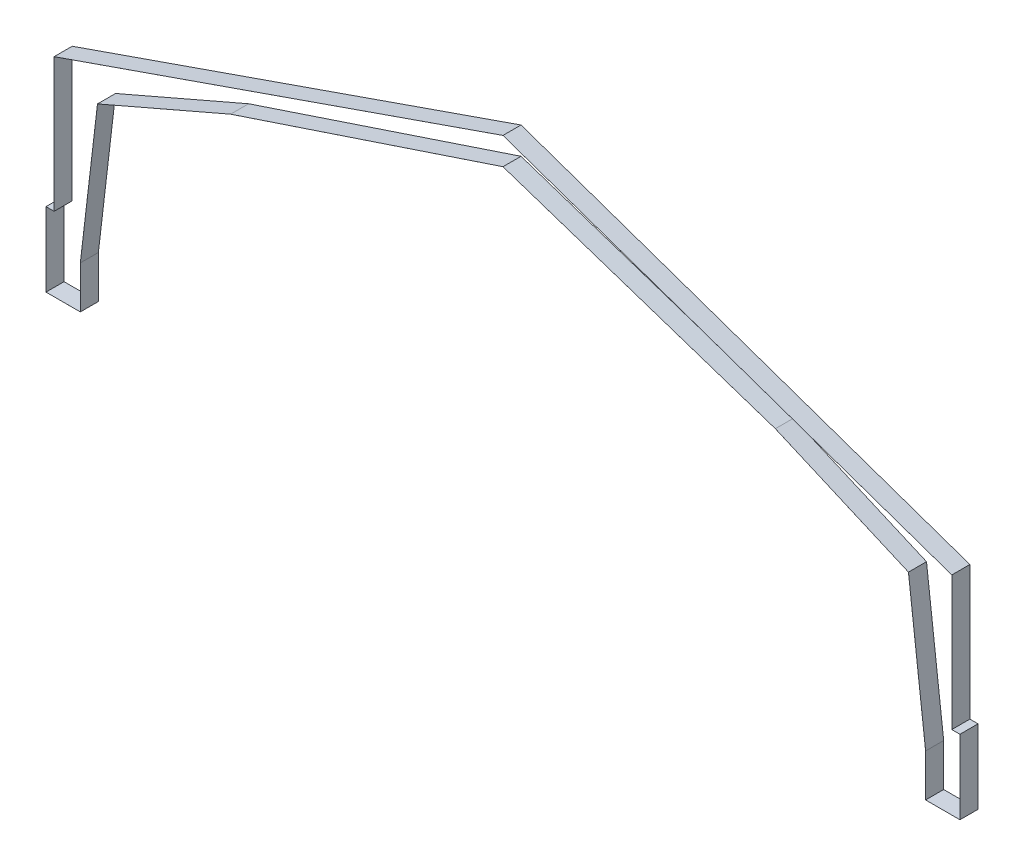
SolidWorks part; units mm, degrees
ref_plane "Alzado" through (0, 0, 0) normal (0, 0, 1) x (1, 0, 0)
ref_plane "Planta" through (0, 0, 0) normal (0, 1, 0) x (1, 0, 0)
ref_plane "Vista lateral" through (0, 0, 0) normal (1, 0, 0) x (0, 0, -1)
sketch "Croquis1" plane through (0, 0, 0) normal (0, 0, 1) x (1, 0, 0)
  line L0 (1447.8, 5308.6) -> (5191.7017, 6929.9999)
  line L1 (5191.7017, 6929.9999) -> (12852.4, 9480.804)
  line L2 (1447.8, 5308.6) -> (965.2, 1193.8)
  line L3 (12852.4, 9480.804) -> (12852.4, 12181.3588) construction
  line L11 (12852.4, 10242.804) -> (228.6, 5849.4967)
  line L12 (0, 2082.8) -> (0, 0)
  line L13 (0, 0) -> (965.2, 0)
  line L14 (965.2, 1193.8) -> (965.2, 0)
  line L15 (0, 2082.8) -> (228.6, 2082.8)
  line L16 (228.6, 2082.8) -> (228.6, 5849.4967)
  line L17 (25704.8, 2082.8) -> (25476.2, 2082.8)
  line L18 (25704.8, 2082.8) -> (25704.8, 0)
  line L19 (24739.6, 1193.8) -> (24739.6, 0)
  line L20 (25704.8, 0) -> (24739.6, 0)
  line L21 (24257, 5308.6) -> (24739.6, 1193.8)
  line L22 (25476.2, 2082.8) -> (25476.2, 5849.4967)
  line L23 (24257, 5308.6) -> (20513.0983, 6929.9999)
  line L24 (12852.4, 10242.804) -> (25476.2, 5849.4967)
  line L25 (20513.0983, 6929.9999) -> (12852.4, 9480.804)
  line L26 (1447.8, 5308.6) -> (1447.8, 6273.8) construction
  line L27 (24257, 5308.6) -> (24257, 6273.8) construction
  dimension "D1" = 762
  dimension "D2" = 2082.8
  dimension "D3" = 5
  dimension "D4" = 4079.9188
  dimension "D5" = 5308.6
  dimension "D6" = 965.2
  dimension "D7" = 1193.8
  dimension "D8" = 4172.204
  dimension "D9" = 228.6
  dimension "D10" = 965.2
  dimension "D11" = 23774.4
  dimension "D12" = 1219.2
extrude "Extruir-Lámina1" add sketch "Croquis1" along normal mid plane 508 thin
